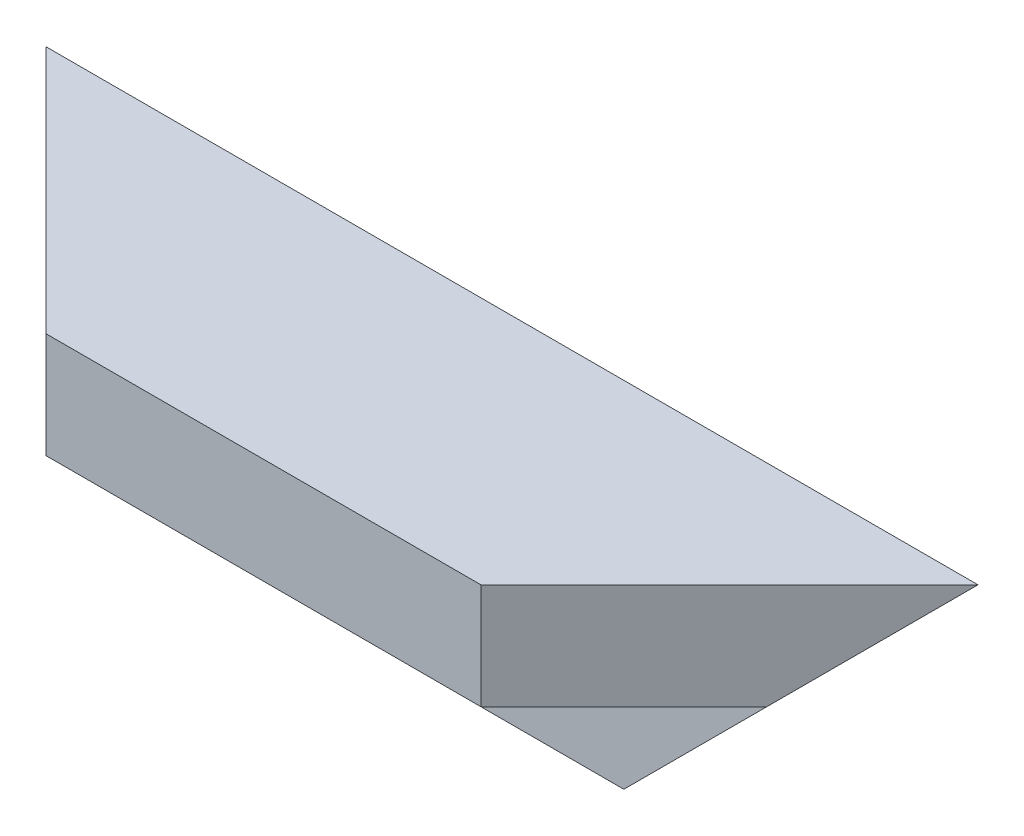
SolidWorks part; units mm, degrees
ref_plane "Plan de face" through (0, 0, 0) normal (0, 0, 1) x (1, 0, 0)
ref_plane "Plan de dessus" through (0, 0, 0) normal (0, 1, 0) x (1, 0, 0)
ref_plane "Plan de droite" through (0, 0, 0) normal (1, 0, 0) x (0, 0, -1)
sketch "Esquisse1" plane through (0, 0, 0) normal (1, 0, 0) x (0, 0, -1)
  line L0 (0, 0) -> (-40, 0)
  line L1 (-40, 0) -> (-40, -17)
  line L2 (-40, -17) -> (-17, -17)
  line L3 (-17, -17) -> (-17, -40)
  line L4 (-17, -40) -> (0, -40)
  line L5 (0, -40) -> (0, 0)
  dimension "D1" = 40
  dimension "D2" = 17
extrude "Boss.-Extru.1" add sketch "Esquisse1" along normal blind 150
sketch "Esquisse2" plane through (0, 0, 0) normal (0, 1, 0) x (1, 0, 0)
  line L0 (150, 0) -> (110, -40)
  line L1 (150, -40) -> (0, -40) construction
  line L2 (110, -40) -> (150, -40)
  line L3 (150, -40) -> (150, 0)
  line L4 (0, 0) -> (0, -40)
  line L5 (0, -40) -> (40, -40)
  line L6 (40, -40) -> (0, 0)
extrude "Enlèv. mat.-Extru.1" cut sketch "Esquisse2" against normal through all
sketch "Esquisse3" plane through (0, 0, 0) normal (0, 0, -1) x (-1, 0, 0)
  line L0 (-150, 0) -> (-110, -40)
  line L1 (-150, -40) -> (0, -40) construction
  line L2 (-110, -40) -> (-150, -40)
  line L3 (-150, -40) -> (-150, 0)
  line L4 (-40, -40) -> (0, -40)
  line L5 (0, -40) -> (0, 0)
  line L6 (0, 0) -> (-40, -40)
extrude "Enlèv. mat.-Extru.2" cut sketch "Esquisse3" against normal through all
